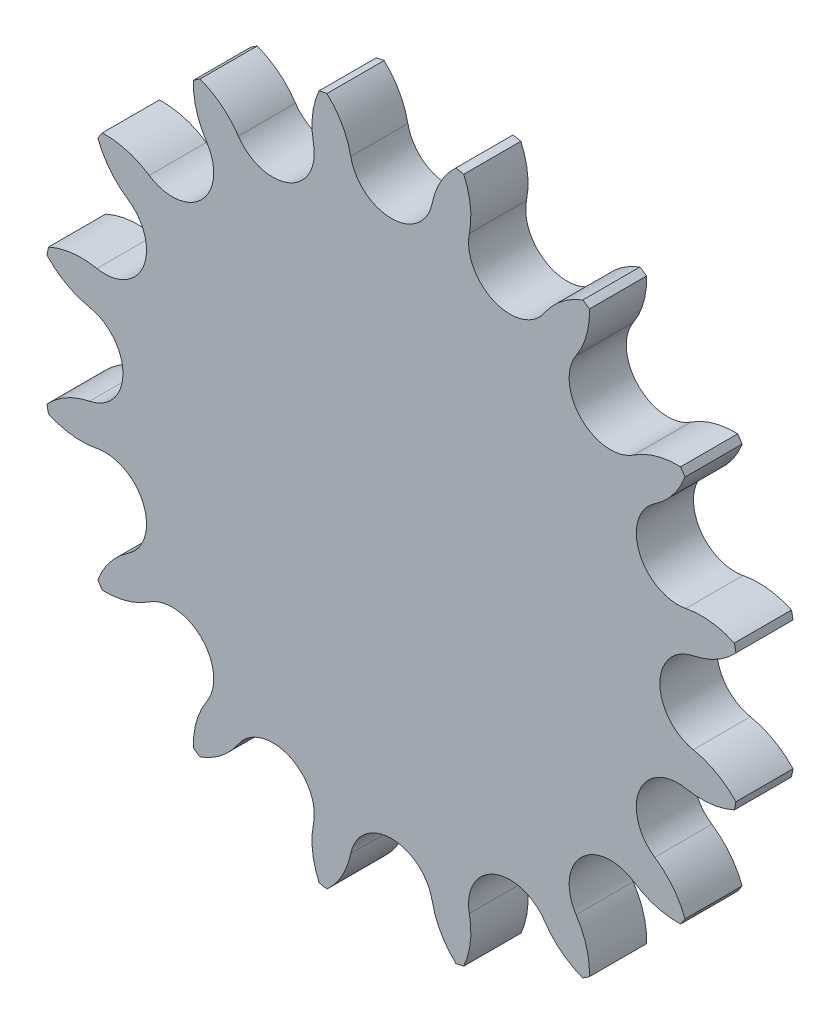
SolidWorks part; units mm, degrees
material "AISI 1020"
ref_plane "Спереди" through (0, 0, 0) normal (0, 0, 1) x (1, 0, 0)
ref_plane "Сверху" through (0, 0, 0) normal (0, 1, 0) x (1, 0, 0)
ref_plane "Справа" through (0, 0, 0) normal (1, 0, 0) x (0, 0, -1)
sketch "Эскиз1" plane through (0, 0, 0) normal (0, 0, 1) x (1, 0, 0)
  line L4 (0, 0) -> (0, 32.549)
  line L5 (0, 32.549) -> (12.456, 30.0714)
  line L6 (12.456, 30.0714) -> (0, 0)
  circle A1 centre (0, 32.549) radius 4.255
  circle A2 centre (12.456, 30.0714) radius 4.255
  circle A3 centre (0, 0) radius 36.804 construction
  dimension "D6" = 8.51
  dimension "D1" = 73.6081
  dimension "D5" = 22.5
  dimension "D7" = 12.7
sketch "Эскиз2" plane through (0, 0, 0) normal (0, 0, 1) x (1, 0, 0)
  line L0 (0, 0) -> (0, 28.194)
  line L1 (0, 0) -> (10.7894, 26.0479)
  line L4 (12.456, 30.0714) -> (0, 0) construction
  arc A0 (8.1847, 30.921) -> (7.5924, 36.0124) centre (0, 32.549) ccw
  arc A1 (0, 36.804) -> (14.0843, 34.0025) centre (0, 0) cw construction
  circle A2 centre (0, 32.549) radius 4.255 construction
  circle A3 centre (12.456, 30.0714) radius 4.255 construction
  circle A5 centre (0, 32.549) radius 4.355
  arc A6 (0, 28.194) -> (4.2713, 31.6994) centre (0, 32.549) ccw
  arc A7 (6.7669, 36.1766) -> (4.2713, 31.6994) centre (12.456, 30.0714) ccw
  circle A8 centre (12.456, 30.0714) radius 4.355
  arc A9 (8.1847, 30.921) -> (10.7894, 26.0479) centre (12.456, 30.0714) ccw
  arc A10 (6.7669, 36.1766) -> (7.5924, 36.0124) centre (0, 0) cw
  dimension "D1" = 0.1
  dimension "D2" = 0.1
extrude "Бобышка-Вытянуть1" add sketch "Эскиз2" along normal blind 6
pattern_circular "Круговой массив1" count 16 over 360 about axis through (0, 0, 0) along (0, 0, 1) of "Бобышка-Вытянуть1"
sketch "Эскиз3" plane through (0, 0, 6) normal (0, 0, 1) x (1, 0, 0)
  line L0 (0, 0) -> (0, 30) construction
  line L1 (0, 0) -> (25.9808, 15) construction
  circle A0 centre (0, 0) radius 17.5
  circle A1 centre (0, 0) radius 30 construction
  circle A2 centre (0, 30) radius 4
  circle A3 centre (25.9808, 15) radius 4
  circle A4 centre (25.9808, -15) radius 4
  circle A5 centre (0, -30) radius 4
  circle A6 centre (-25.9808, -15) radius 4
  circle A7 centre (-25.9808, 15) radius 4
  dimension "D1" = 35
  dimension "D2" = 60
  dimension "D3" = 8
  dimension "D5" = 60
  dimension "D6" = 30
  dimension "D4" = 6
extrude "Вырез-Вытянуть1" [suppressed] cut sketch "Эскиз3" against normal through all
equation "\"D5@Эскиз1\"=360/\"_kol-vo\""
equation "\"_kol-vo\"= 16"
equation "\"_Pitch\"=12.7"
equation "\"_d1_max\"= 8.51"
equation "\"_d1_min\"= 7.75"
equation "\"_d2_max\"= 4.45"
equation "\"_T_max\"= 1.6"
equation "\"_h2\"= 11.8"
equation "\"_L_max\"= 16.85"
equation "\"_Lc_max\"= 18.1"
equation "\"D6@Эскиз1\"=\"_d1_max\""
equation "\"D1@Круговой массив1\"=\"_kol-vo\""
equation "\"D7@Эскиз1\"=\"_Pitch\""
